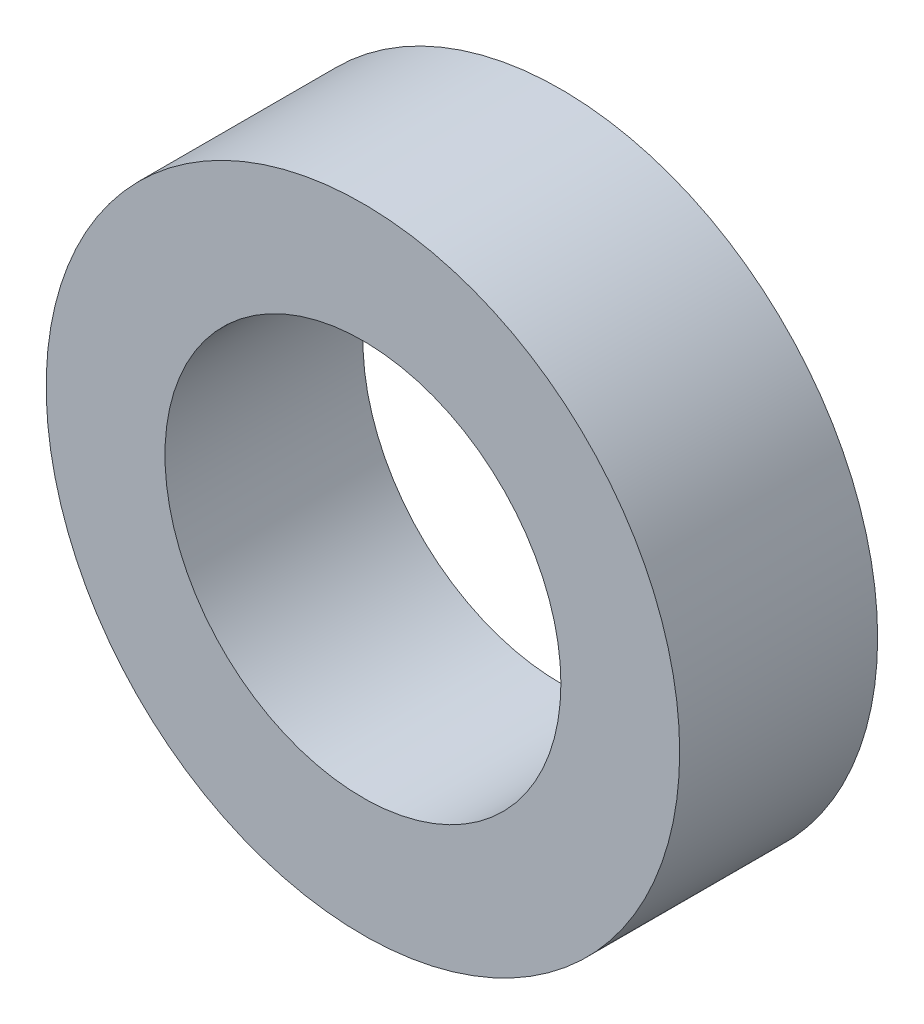
SolidWorks part; units mm, degrees
ref_plane "前视基准面" through (0, 0, 0) normal (0, 0, 1) x (1, 0, 0)
ref_plane "上视基准面" through (0, 0, 0) normal (0, 1, 0) x (1, 0, 0)
ref_plane "右视基准面" through (0, 0, 0) normal (1, 0, 0) x (0, 0, -1)
sketch "草图1" plane through (0, 0, 0) normal (0, 0, 1) x (1, 0, 0)
  circle A0 centre (0, 0) radius 4
  circle A1 centre (0, 0) radius 2.5
  dimension "D1" = 8
  dimension "D2" = 5
extrude "凸台-拉伸1" add sketch "草图1" along normal blind 2.5
